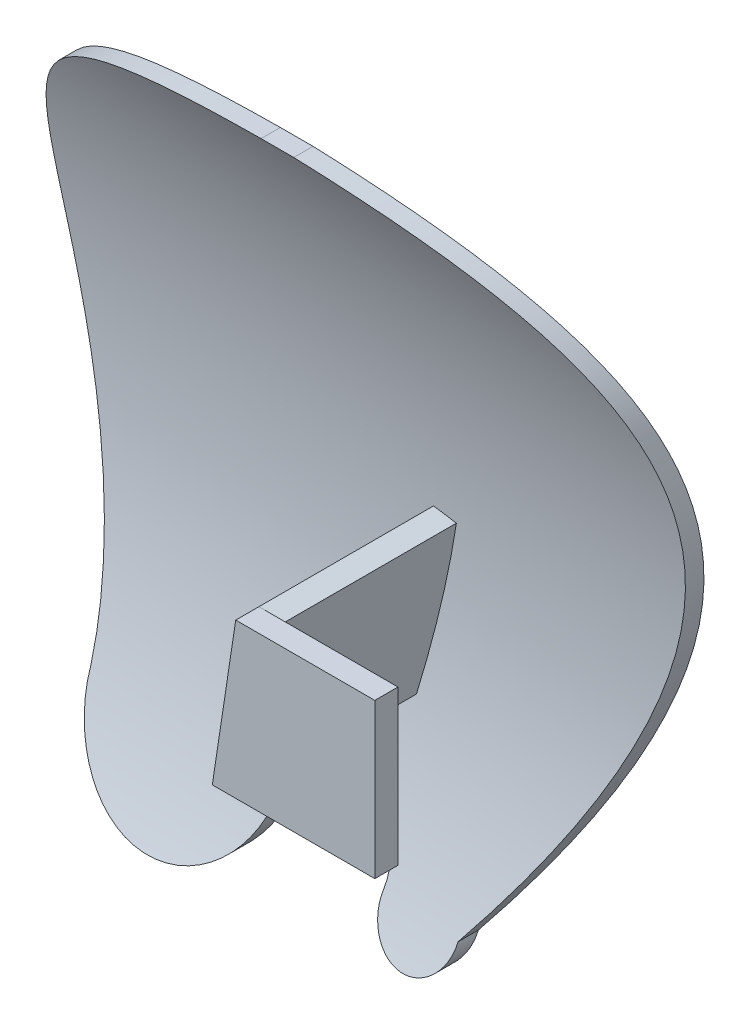
SolidWorks part; units mm, degrees
ref_plane "Front Plane" through (0, 0, 0) normal (0, 0, 1) x (1, 0, 0)
ref_plane "Top Plane" through (0, 0, 0) normal (0, 1, 0) x (1, 0, 0)
ref_plane "Right Plane" through (0, 0, 0) normal (1, 0, 0) x (0, 0, -1)
sketch "Sketch2" plane through (0, 0, 0) normal (0, 0, 1) x (1, 0, 0)
  line L1 (-45, 45) -> (45, 45)
  line L2 (-45, 45) -> (-45, -45)
  line L3 (-45, -45) -> (45, -45)
  line L4 (45, 45) -> (45, -45)
  line L5 (-45, 45) -> (45, -45) construction
  line L6 (-45, -45) -> (45, 45) construction
  point P0 (0, 0)
  dimension "D1" = 90
  dimension "D2" = 90
extrude "Boss-Extrude1" add sketch "Sketch2" along normal blind 20
sketch "Sketch3" plane through (0, 0, 0) normal (1, 0, 0) x (0, 0, -1)
  line L0 (-20, 45) -> (0, 45) construction
  line L1 (-20, -45) -> (0, -45) construction
  line L3 (0, 45) -> (-20, 45)
  line L4 (0, 45) -> (0, -45)
  line L5 (0, -45) -> (-20, -45)
  line L6 (-20, 45) -> (-20, -45)
  spline S0 degree 2 poles (-20, 45) (4.2276, 5.0347) (-20, -45) knots 0 0 0 1 1 1
  spline S1 degree 2 poles (-17.5, 45) (6.7261, 3.0938) (-17.5, -45) knots 0 0 0 1 1 1
  dimension "D1" = 2.5
  dimension "D2" = 2.5
extrude "Cut-Extrude1" cut sketch "Sketch3" along normal through all both and the other way through all contours L3 S1 L5 L4 | S0 L6
sketch "Sketch4" plane through (0, 0, 0) normal (0, 0, 1) x (1, 0, 0)
  line L0 (0, -59.8586) -> (0, 59.8586) construction
  line L1 (45, 45) -> (-45, 45) construction
  line L3 (45, 45) -> (-45, 45)
  line L4 (45, 45) -> (45, -45)
  line L5 (45, -45) -> (-45, -45)
  line L6 (-45, 45) -> (-45, -45)
  circle A0 centre (0, -34.4737) radius 7.5
  circle A1 centre (-19.6878, -30.9537) radius 12.5
  circle A2 centre (12.3751, -36.2367) radius 5
  spline S0 degree 3 poles (17.3751, -36.2367) (37.1151, -9.0918) (61.513, 39.3556) (0, 45) knots 0 0 0 0 1 1 1 1
  spline S1 degree 3 poles (-32.1878, -30.9537) (-34.1516, -0.2959) (-65.4777, 46.0445) (0, 45) knots 0 0 0 0 1 1 1 1
  point P4 (0, 0)
  dimension "D1" = 15
  dimension "D2" = 25
  dimension "D3" = 10
extrude "Cut-Extrude2" cut sketch "Sketch4" against normal through all both and the other way through all contours L0 L5 L4 L3 S0 A2 A0 | L5 L0 A0 A1 S1 L3 L6 | A0 L0 | L0 A0
sketch "Sketch5" plane through (0, 0, 0) normal (0, 0, 1) x (1, 0, 0)
  line L0 (5.9879, -17.1439) -> (8.9535, 2.4062)
  line L1 (8.9535, 2.4062) -> (5.9874, 2.8561)
  line L2 (5.9874, 2.8561) -> (2.9536, -17.1439)
  line L3 (2.9536, -17.1439) -> (5.9879, -17.1439)
  dimension "D1" = 20
  dimension "D2" = 3
extrude "Boss-Extrude2" add sketch "Sketch5" along normal blind 26 from offset 7.5
sketch "Sketch6" plane through (0, 0, 0) normal (1, 0, 0) x (0, 0, -1)
  line L0 (-33.5, -17.1439) -> (-10.0921, -17.1439) construction
  line L1 (-33.5, 2.8561) -> (-30.5, 2.8561)
  line L2 (-33.5, 2.8561) -> (-33.5, -17.1439)
  line L3 (-33.5, -17.1439) -> (-30.5, -17.1439)
  line L4 (-30.5, 2.8561) -> (-30.5, -17.1439)
  dimension "D1" = 3
extrude "Boss-Extrude3" add sketch "Sketch6" along normal blind 20 from offset 4
sketch "Sketch7" plane through (0, 0, 0) normal (0, 0, 1) x (1, 0, 0)
  line L0 (4, -10.2457) -> (5.9874, 2.8561)
  line L1 (5.9874, 2.8561) -> (3.0196, 2.8561)
  line L2 (3.0196, 2.8561) -> (3.5821, -13.0008)
  line L3 (5.9874, 2.8561) -> (2.9536, -17.1439) construction
  line L4 (3.5821, -13.0008) -> (4, -10.2457)
extrude "Cut-Extrude3" cut sketch "Sketch7" along normal blind 10 from offset 30
